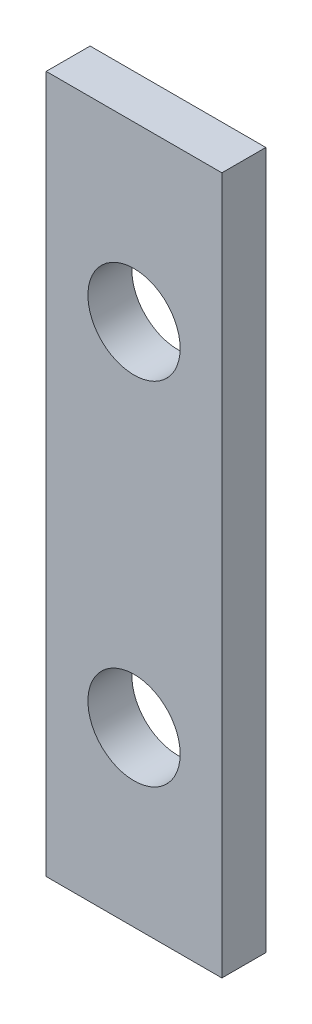
SolidWorks part; units mm, degrees
ref_plane "Front Plane" through (0, 0, 0) normal (0, 0, 1) x (1, 0, 0)
ref_plane "Top Plane" through (0, 0, 0) normal (0, 1, 0) x (1, 0, 0)
ref_plane "Right Plane" through (0, 0, 0) normal (1, 0, 0) x (0, 0, -1)
sketch "Sketch3" plane through (0, 0, 0) normal (0, 1, 0) x (1, 0, 0)
  line L0 (6.282, 2.5073) -> (-1.718, 2.5073)
  line L1 (6.282, 2.5073) -> (6.282, 4.5073)
  line L2 (-1.718, 2.5073) -> (-1.718, 4.5073)
  line L3 (6.282, 4.5073) -> (-1.718, 4.5073)
  line L4 (6.282, 2.5073) -> (-1.718, 4.5073) construction
  line L5 (-1.718, 2.5073) -> (6.282, 4.5073) construction
  point P1 (2.282, 3.5073)
  dimension "D1" = 2
  dimension "D2" = 8
extrude "Boss-Extrude2" add sketch "Sketch3" along normal blind 31.75 separate body
sketch "Sketch4" plane through (0, 0, -2.5073) normal (0, 0, 1) x (1, 0, 0)
  circle A15 centre (2.282, 7.875) radius 2.1
  circle A16 centre (2.282, 23.875) radius 2.1
  dimension "D1" = 4.2
  dimension "D2" = 4.2
extrude "Cut-Extrude1" cut sketch "Sketch4" against normal through all
